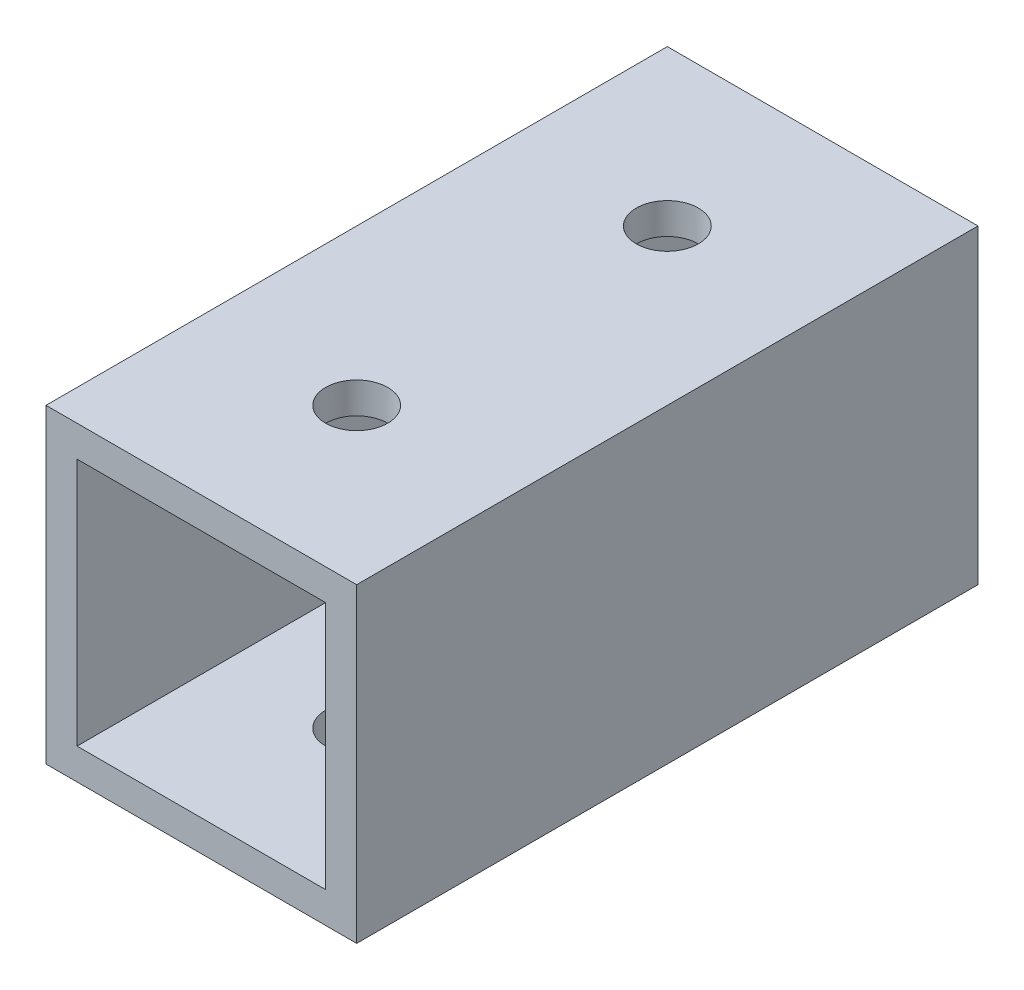
SolidWorks part; units mm, degrees
material "1060 合金"
ref_plane "正面" through (0, 0, 0) normal (0, 0, 1) x (1, 0, 0)
ref_plane "平面" through (0, 0, 0) normal (0, 1, 0) x (1, 0, 0)
ref_plane "右側面" through (0, 0, 0) normal (1, 0, 0) x (0, 0, -1)
sketch "ｽｹｯﾁ1" plane through (0, 0, 0) normal (0, 0, 1) x (1, 0, 0)
  line L1 (-7.0101, 7.7326) -> (7.9899, 7.7326)
  line L2 (-7.0101, 7.7326) -> (-7.0101, -7.2674)
  line L3 (-7.0101, -7.2674) -> (7.9899, -7.2674)
  line L4 (7.9899, 7.7326) -> (7.9899, -7.2674)
  line L9 (-5.5101, 6.2326) -> (6.4899, 6.2326)
  line L10 (-5.5101, 6.2326) -> (-5.5101, -5.7674)
  line L11 (-5.5101, -5.7674) -> (6.4899, -5.7674)
  line L12 (6.4899, 6.2326) -> (6.4899, -5.7674)
  dimension "D1" = 15
  dimension "D2" = 15
  dimension "D3" = 1.5
  dimension "D4" = 1.5
  dimension "D5" = 12
  dimension "D6" = 12
extrude "ﾎﾞｽ - 押し出し2" add sketch "ｽｹｯﾁ1" along normal blind 30
sketch "ｽｹｯﾁ2" plane through (0, 7.7326, 0) normal (0, 1, 0) x (1, 0, 0)
  line L0 (0.4899, -30) -> (0.4899, -22.5)
  line L1 (7.9899, -30) -> (-7.0101, -30) construction
  circle A0 centre (0.4899, -22.5) radius 1.5
  dimension "D1" = 7.5
extrude "ｶｯﾄ - 押し出し1" cut sketch "ｽｹｯﾁ2" against normal blind 20
sketch "ｽｹｯﾁ3" plane through (0, 7.7326, 0) normal (0, 1, 0) x (1, 0, 0)
  line L0 (0.4899, 0) -> (0.4899, -7.5)
  line L1 (7.9899, 0) -> (-7.0101, 0) construction
  circle A0 centre (0.4899, -7.5) radius 1.5
  dimension "D1" = 7.5
extrude "ｶｯﾄ - 押し出し2" cut sketch "ｽｹｯﾁ3" against normal blind 10
